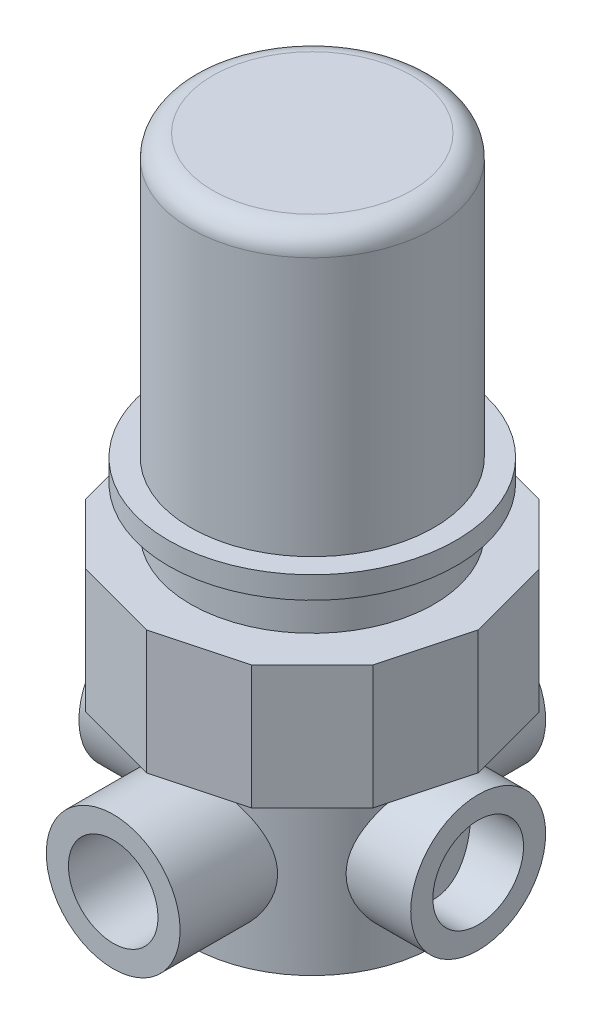
SolidWorks part; units mm, degrees
ref_plane "Front Plane" through (0, 0, 0) normal (0, 0, 1) x (1, 0, 0)
ref_plane "Top Plane" through (0, 0, 0) normal (0, 1, 0) x (1, 0, 0)
ref_plane "Right Plane" through (0, 0, 0) normal (1, 0, 0) x (0, 0, -1)
sketch "Sketch1" plane through (0, 0, 0) normal (0, 0, 1) x (1, 0, 0)
  line L0 (0, 73.914) -> (0, 0) construction
  line L1 (0, 73.914) -> (13.97, 73.914)
  line L2 (13.97, 73.914) -> (13.97, 41.656)
  line L3 (13.97, 41.656) -> (16.51, 41.656)
  line L4 (16.51, 41.656) -> (16.51, 39.116)
  line L5 (16.51, 39.116) -> (13.97, 39.116)
  line L6 (13.97, 39.116) -> (13.97, 34.036)
  line L7 (13.97, 34.036) -> (19.05, 34.036)
  line L8 (19.05, 34.036) -> (19.05, 19.812)
  line L9 (19.05, 19.812) -> (13.97, 19.812)
  line L10 (13.97, 19.812) -> (13.97, 0)
  line L11 (13.97, 0) -> (0, 0)
  line L12 (0, 73.914) -> (0, 0)
  point P11 (13.97, 9.906)
  dimension "D1" = 73.914
  dimension "D2" = 24.13
  dimension "D3" = 64.008
  dimension "D4" = 38.1
  dimension "D5" = 27.94
  dimension "D6" = 27.94
  dimension "D7" = 2.54
  dimension "D8" = 2.54
  dimension "D9" = 5.08
revolve "Revolve1" add sketch "Sketch1" angle 360 about L0
sketch "Sketch2" plane through (0, 34.036, 0) normal (0, 1, 0) x (1, 0, 0)
  line L1 (0, 19.05) -> (-9.525, 16.4978)
  line L2 (-9.525, 16.4978) -> (-16.4978, 9.525)
  line L3 (-16.4978, 9.525) -> (-19.05, 0)
  line L4 (-19.05, 0) -> (-16.4978, -9.525)
  line L5 (-16.4978, -9.525) -> (-9.525, -16.4978)
  line L6 (-9.525, -16.4978) -> (0, -19.05)
  line L7 (0, -19.05) -> (9.525, -16.4978)
  line L8 (9.525, -16.4978) -> (16.4978, -9.525)
  line L9 (16.4978, -9.525) -> (19.05, 0)
  line L10 (19.05, 0) -> (16.4978, 9.525)
  line L11 (16.4978, 9.525) -> (9.525, 16.4978)
  line L12 (9.525, 16.4978) -> (0, 19.05)
  circle A0 centre (0, 0) radius 18.4009 construction
  circle A1 centre (0, 0) radius 19.05 construction
  circle A2 centre (0, 0) radius 19.05
  circle M2 centre (0, 0) radius 19.05
extrude "Cut-Extrude1" cut sketch "Sketch2" against normal up to next contours L2 M2 | L3 M2 | L4 M2 | L5 M2 | L6 M2 | L7 M2 | L8 M2 | L9 M2 | L10 M2 | L11 M2 | L12 M2 | L1 M2 | A2
ref_plane "Plane1" through (0, 0, 13.97) normal (0, 0, 1) x (1, 0, 0)
sketch "Sketch3" plane through (0, 0, 13.97) normal (0, 0, 1) x (1, 0, 0)
  line L0 (0, 0) -> (0, 19.812) construction
  line L1 (-13.97, 19.812) -> (13.97, 19.812) construction
  circle A0 centre (0, 9.906) radius 5.1435
  circle A1 centre (0, 9.906) radius 7.6835
  point P8 (0, 9.906)
  dimension "D1" = 10.287
  dimension "D2" = 2.54
extrude "Boss-Extrude1" add sketch "Sketch3" along normal blind 8.89 and the other way up to surface (8.89 mm away)
ref_plane "Plane2" through (13.97, 0, 0) normal (1, 0, 0) x (0, 0, -1)
sketch "Sketch4" plane through (13.97, 0, 0) normal (1, 0, 0) x (0, 0, -1)
  line L0 (0, 19.812) -> (0, 0) construction
  line L1 (-13.97, 19.812) -> (13.97, 19.812) construction
  circle A0 centre (0, 9.906) radius 5.207
  circle A1 centre (0, 9.906) radius 7.747
  point P8 (0, 9.906)
  dimension "D1" = 10.414
  dimension "D2" = 2.54
extrude "Boss-Extrude2" add sketch "Sketch4" along normal blind 5.08 and the other way up to surface
pattern_circular "CirPattern1" count 4 over 360 about axis through (0, 73.914, 0) along (0, 1, 0) skipping 1 of "Boss-Extrude2"
fillet "Fillet1" radius 2.54 1 edges at (0, 73.914, 13.97)
